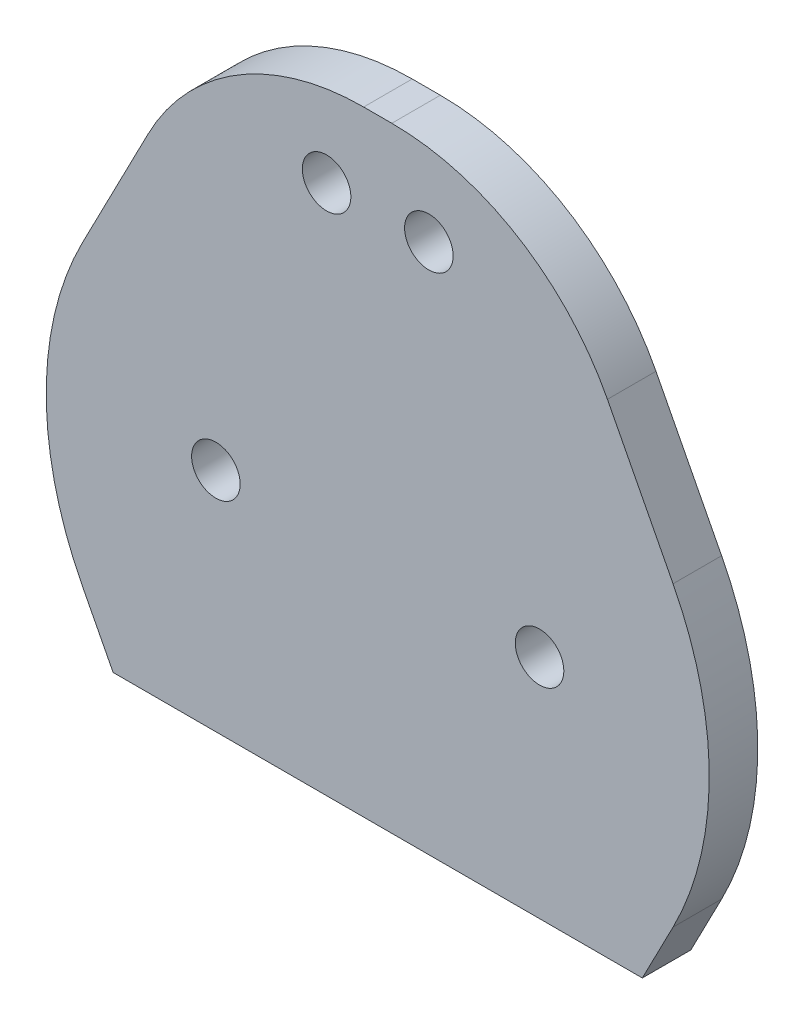
SolidWorks part; units mm, degrees
material "3.0205 (EN-AW 1200)"
ref_plane "Piano frontale" through (0, 0, 0) normal (0, 0, 1) x (1, 0, 0)
ref_plane "Piano superiore" through (0, 0, 0) normal (0, 1, 0) x (1, 0, 0)
ref_plane "Piano destro" through (0, 0, 0) normal (1, 0, 0) x (0, 0, -1)
sketch "Schizzo1" plane through (0, 0, 0) normal (0, 0, 1) x (1, 0, 0)
  line L0 (-54.8681, 0) -> (41.6416, 0) construction
  line L1 (0, 0) -> (-6.8404, 18.7939) construction
  line L2 (-10.0004, -25.7598) -> (-10.0004, 32.5728) construction
  line L3 (12.9996, 24) -> (12.9996, -14)
  line L4 (-13.1604, 18.7939) -> (-20.0008, 0) construction
  line L6 (12.9996, -14) -> (-33.0004, -14)
  line L7 (-33.0004, -14) -> (-33.0004, 24)
  line L8 (-33.0004, 24) -> (12.9996, 24)
  circle A0 centre (-6.8404, 18.7939) radius 1.5
  circle A1 centre (0, 0) radius 1.5
  circle A2 centre (-20.0008, 0) radius 1.5
  circle A3 centre (-13.1604, 18.7939) radius 1.5
  dimension "D6" = 38
  dimension "D3" = 3
  dimension "D5" = 3
  dimension "D7" = 24
  dimension "D1" = 20
  dimension "D2" = 70
  dimension "D4" = 46
  dimension "D8" = 6.32
  dimension "D9" = 23
extrude "Estrusione-Estrusione3" add sketch "Schizzo1" along normal blind 3
sketch "Schizzo4" plane through (0, 0, 3) normal (0, 0, 1) x (1, 0, 0)
  line L0 (-10.0004, 24) -> (-20.0004, 24)
  line L1 (12.9996, 24) -> (-33.0004, 24) construction
  line L2 (-20.0004, 24) -> (-33.0004, -1.1396)
  line L3 (-33.0004, 24) -> (-33.0004, -14) construction
  line L4 (-33.0004, -1.1396) -> (-26.3501, -14)
  line L5 (-33.0004, -14) -> (12.9996, -14) construction
  line L6 (-26.3501, -14) -> (6.3493, -14)
  line L7 (6.3493, -14) -> (12.9996, -1.1396)
  line L8 (12.9996, -14) -> (12.9996, 24) construction
  line L9 (12.9996, -1.1396) -> (-0.0004, 24)
  line L10 (-0.0004, 24) -> (-20.0004, 24)
  line M8 (-33.0004, -14) -> (12.9996, -14)
  line M9 (12.9996, -14) -> (12.9996, 24)
  line M10 (12.9996, 24) -> (-33.0004, 24)
  line M11 (-33.0004, 24) -> (-33.0004, -14)
  dimension "D1" = 10
  dimension "D2" = 28.3019
  dimension "D3" = 10
extrude "Taglio-Estrusione1" cut sketch "Schizzo4" against normal blind 3 contours L2 M10 M11 | L9 M9 M10 | L4 M11 M8 | L7 M8 M9
fillet "Raccordo1" radius 15 1 edges at (-0.0004, 24, 1.5)
fillet "Raccordo2" radius 15 1 edges at (-20.0004, 24, 1.5)
fillet "Raccordo3" radius 20 1 edges at (12.9996, -1.1396, 1.5)
fillet "Raccordo4" radius 20 1 edges at (-33.0004, -1.1396, 1.5)
